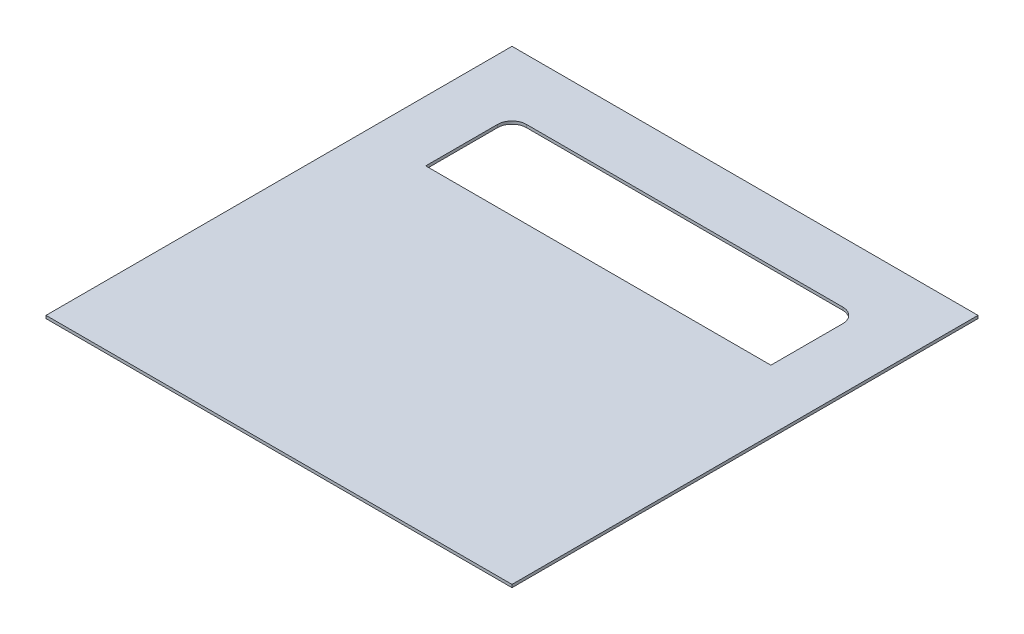
SolidWorks part; units mm, degrees
ref_plane "前视基准面" through (0, 0, 0) normal (0, 0, 1) x (1, 0, 0)
ref_plane "上视基准面" through (0, 0, 0) normal (0, 1, 0) x (1, 0, 0)
ref_plane "右视基准面" through (0, 0, 0) normal (1, 0, 0) x (0, 0, -1)
sketch "草图1" plane through (0, 0, 0) normal (0, 1, 0) x (1, 0, 0)
  line L1 (-81, -81) -> (81, -81)
  line L2 (-81, -81) -> (-81, 81)
  line L3 (-81, 81) -> (81, 81)
  line L4 (81, -81) -> (81, 81)
  line L5 (-81, -81) -> (81, 81) construction
  line L6 (-81, 81) -> (81, -81) construction
  point P0 (0, 0)
  dimension "D1" = 162
  dimension "D2" = 162
extrude "凸台-拉伸1" add sketch "草图1" along normal blind 1
sketch "草图2" plane through (0, 0, 0) normal (0, -1, 0) x (1, 0, 0)
  line L1 (-60, -30) -> (60, -30)
  line L2 (-60, -30) -> (-60, -60)
  line L3 (-60, -60) -> (60, -60)
  line L4 (60, -30) -> (60, -60)
  line L5 (-60, -30) -> (60, -60) construction
  line L6 (-60, -60) -> (60, -30) construction
  point P0 (0, -45)
  point P5 (0, 0)
  dimension "D1" = 45
  dimension "D2" = 120
  dimension "D3" = 30
extrude "切除-拉伸1" cut sketch "草图2" against normal up to next
fillet "圆角1" radius 5 2 edges at (-60, 0.5, -60) (60, 0.5, -60)
